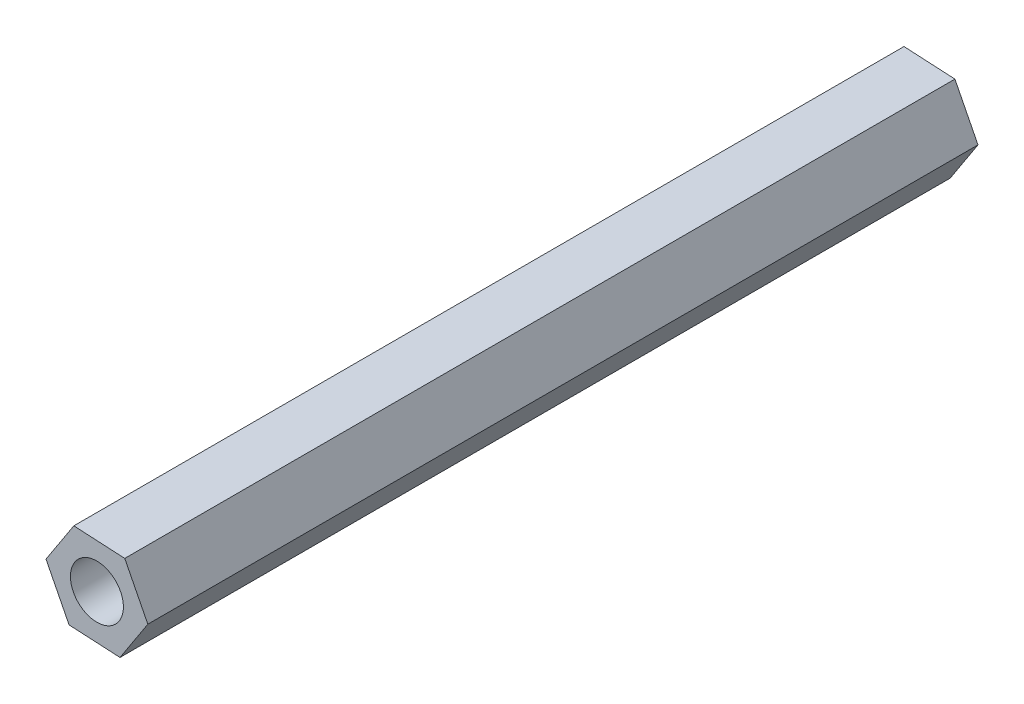
SolidWorks part; units mm, degrees
ref_plane "Front Plane" through (0, 0, 0) normal (0, 0, 1) x (1, 0, 0)
ref_plane "Top Plane" through (0, 0, 0) normal (0, 1, 0) x (1, 0, 0)
ref_plane "Right Plane" through (0, 0, 0) normal (1, 0, 0) x (0, 0, -1)
sketch "Sketch1" plane through (0, 0, 0) normal (0, 0, 1) x (1, 0, 0)
  line L1 (1.5755, 2.4189) -> (-1.3071, 2.5739)
  line L2 (-1.3071, 2.5739) -> (-2.8826, 0.1549)
  line L3 (-2.8826, 0.1549) -> (-1.5755, -2.4189)
  line L4 (-1.5755, -2.4189) -> (1.3071, -2.5739)
  line L5 (1.3071, -2.5739) -> (2.8826, -0.1549)
  line L6 (2.8826, -0.1549) -> (1.5755, 2.4189)
  circle A0 centre (0, 0) radius 2.5 construction
  dimension "D1" = 5
extrude "Boss-Extrude1" add sketch "Sketch1" along normal blind 47
sketch "Sketch2" plane through (0, 0, 0) normal (0, 0, -1) x (-1, 0, 0)
  circle A0 centre (0, 0) radius 1.5
  dimension "D1" = 3
extrude "Cut-Extrude1" cut sketch "Sketch2" against normal through all
